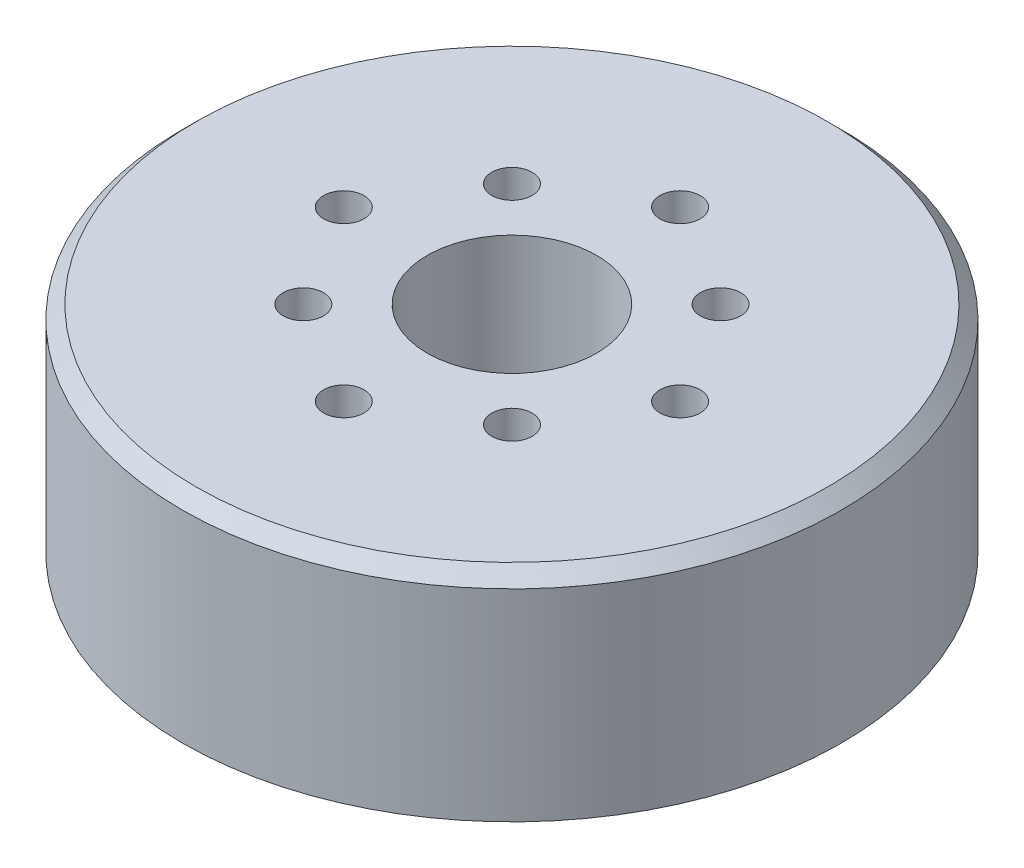
SolidWorks part; units mm, degrees
material "Alliage 1060"
ref_plane "Plan de face" through (0, 0, 0) normal (0, 0, 1) x (1, 0, 0)
ref_plane "Plan de dessus" through (0, 0, 0) normal (0, 1, 0) x (1, 0, 0)
ref_plane "Plan de droite" through (0, 0, 0) normal (1, 0, 0) x (0, 0, -1)
sketch "Esquisse1" plane through (0, 0, 0) normal (0, 1, 0) x (1, 0, 0)
  line L0 (0, 0) -> (0, 24.5) construction
  line L1 (0, 0) -> (17.3241, 17.3241) construction
  circle A0 centre (0, 0) radius 24.5
  circle A1 centre (0, 0) radius 12.5 construction
  circle A2 centre (0, 0) radius 11 construction
  circle A3 centre (0, 12.5) radius 1.5
  circle A4 centre (12.5, 0) radius 1.5
  circle A5 centre (0, -12.5) radius 1.5
  circle A6 centre (-12.5, 0) radius 1.5
  circle A7 centre (7.753, 7.753) radius 1.5
  circle A8 centre (7.753, -7.753) radius 1.5
  circle A9 centre (-7.753, -7.753) radius 1.5
  circle A10 centre (-7.753, 7.753) radius 1.5
  circle A11 centre (0, 0) radius 6.3
  point P16 (0, 0)
  point P27 (0, 0)
  dimension "D1" = 49
  dimension "D2" = 25
  dimension "D3" = 22
  dimension "D4" = 3
  dimension "D7" = 3
  dimension "D9" = 12.6
  dimension "D6" = 45
  dimension "D5" = 4
  dimension "D8" = 4
extrude "Boss.-Extru.1" add sketch "Esquisse1" along normal blind 16
chamfer "Chanfrein1" distance 1 angle 45 1 edges at (0, 16, 24.5)
